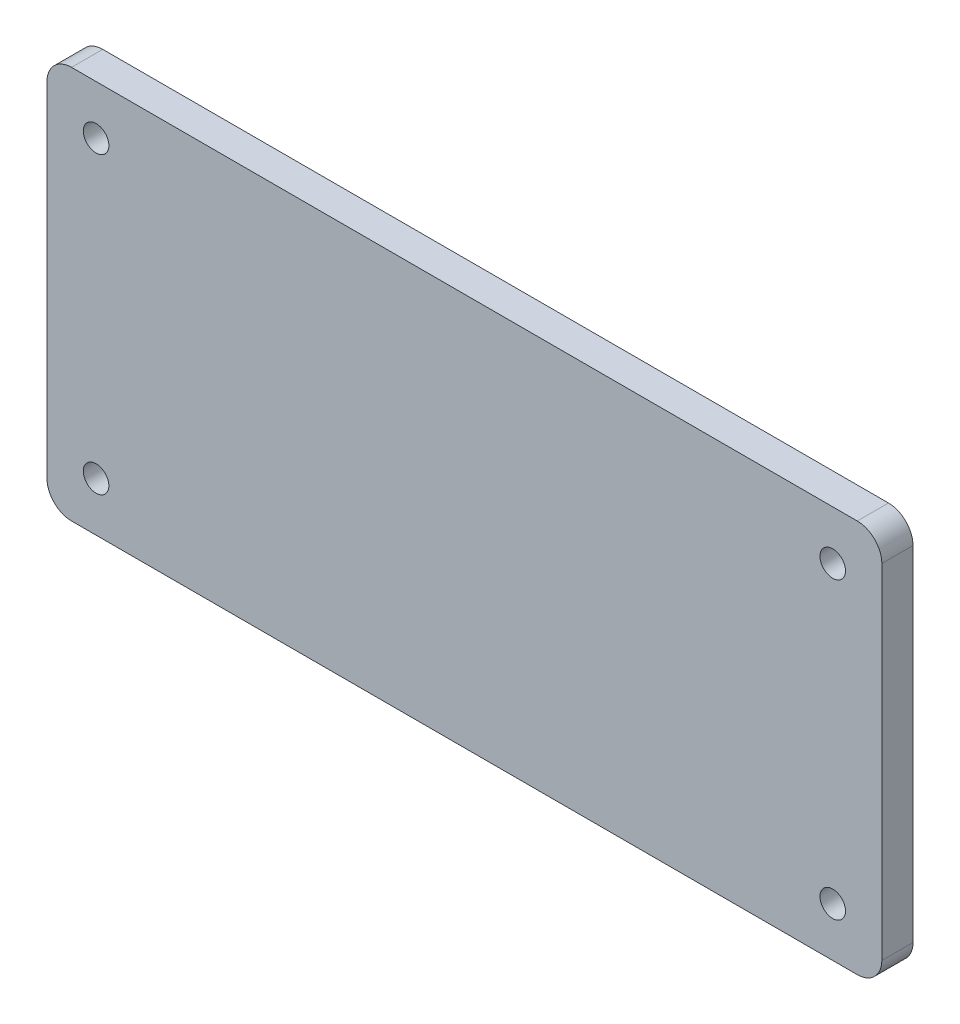
SolidWorks part; units mm, degrees
ref_plane "Front Plane" through (0, 0, 0) normal (0, 0, 1) x (1, 0, 0)
ref_plane "Top Plane" through (0, 0, 0) normal (0, 1, 0) x (1, 0, 0)
ref_plane "Right Plane" through (0, 0, 0) normal (1, 0, 0) x (0, 0, -1)
sketch "Sketch1" plane through (0, 0, 0) normal (0, 0, 1) x (1, 0, 0)
  line L0 (0, 124.4013) -> (0, -139.7481) construction
  line L1 (80, -40) -> (-80, -40)
  line L2 (85, -35) -> (85, 35)
  line L3 (80, 40) -> (-80, 40)
  line L4 (-85, -35) -> (-85, 35)
  line L5 (85, -40) -> (-85, 40) construction
  line L6 (85, 40) -> (-85, -40) construction
  line L7 (232.754, 0) -> (-222.1699, 0) construction
  circle A0 centre (-75, 30) radius 2.6
  circle A1 centre (75, 30) radius 2.6
  circle A2 centre (75, -30) radius 2.6
  circle A3 centre (-75, -30) radius 2.6
  arc A4 (80, 40) -> (85, 35) centre (80, 35) cw
  arc A5 (80, -40) -> (85, -35) centre (80, -35) ccw
  arc A6 (-80, -40) -> (-85, -35) centre (-80, -35) cw
  arc A7 (-85, 35) -> (-80, 40) centre (-80, 35) cw
  point P0 (0, 0)
  dimension "D5" = 5.2
  dimension "D6" = 5
  dimension "D1" = 80
  dimension "D2" = 170
  dimension "D3" = 10
  dimension "D4" = 10
extrude "Boss-Extrude1" add sketch "Sketch1" along normal blind 6.35
sketch "Sketch6" [suppressed] plane through (0, 0, 6.35) normal (0, 0, 1) x (1, 0, 0)
  line L0 (19, 0) -> (-19, 0) construction
  line B0 (-19, 14) -> (19, 14)
  line B1 (19, -14) -> (-19, -14)
  line B2 (19, 14) -> (19, -14)
  line B3 (-19, -14) -> (-19, 14)
  circle B4 centre (-14.5, -12.5) radius 1
  circle B5 centre (17.5, 12.5) radius 1
  line B6 (-19, 14) -> (-19, -14)
  circle B7 centre (-14.5, 12.5) radius 1
  circle B8 centre (17.5, -12.5) radius 1
sketch_block_instance "Block-Single_Motor_Driver_reference-1"
sketch_block "Block-Single_Motor_Driver_reference"
sketch_block_instance "Block-Single_Motor_Driver_reference-3"
sketch "Sketch7" [suppressed] plane through (0, 0, 6.35) normal (0, 0, 1) x (1, 0, 0)
  line B0 (10, 88.2866) -> (10, -79.1784) construction
  line B1 (-30.7948, 22.4079) -> (-30.7948, -19.5021)
  line B2 (-24.4448, -25.8521) -> (42.8652, -25.8521)
  circle B3 centre (-16.1898, 25.5829) radius 1.524
  arc B4 (-30.7948, -19.5021) -> (-24.4448, -25.8521) centre (-24.4448, -19.5021) ccw
  circle B5 centre (49.8502, 22.4079) radius 1.524
  circle B6 centre (49.8502, -19.5021) radius 1.524
  circle B7 centre (-16.1898, -22.6771) radius 1.524
  dimension "D1" = 10
sketch_block_instance "Block-BBB_reference-1"
sketch_block "Block-BBB_reference"
hole_wizard "BBB_mtg_holes" [suppressed] positions "Sketch3" profile "Sketch2" countersink size "M3" standard "ANSI Metric"
sketch "Sketch3" plane through (0, 0, 6.35) normal (0, 0, 1) x (1, 0, 0)
  point P0 (-16.1898, 25.5829)
  point P2 (-16.1898, -22.6771)
  point P4 (49.8502, -19.5021)
  point P6 (49.8502, 22.4079)
sketch "Sketch2" plane through (-16.1898, 25.5829, 6.35) normal (1, 0, 0) x (0, -1, 0)
  line L0 (0, 0) -> (0, 6.35)
  line L1 (0, 6.35) -> (1.7, 6.35)
  line L2 (1.7, 6.35) -> (1.7, 1.45)
  line L3 (1.7, 1.45) -> (3.15, 0)
  line L5 (3.15, 0) -> (0, 0)
  line L6 (-1.7, 1.45) -> (-3.15, 0) construction
  line L11 (0, -6.35) -> (0, 107.95) construction
  dimension "Thru Hole Dia." = 3.4
  dimension "Thru Hole Depth" = 6.35
  dimension "Near C'Sink Dia." = 6.3
  dimension "Near C'Sink Angle" = 90
hole_wizard "Motor_Driver_mtg_holes" [suppressed] positions "Sketch5" profile "Sketch4" countersink size "#0" standard "ANSI Inch"
sketch "Sketch5" plane through (0, 0, 6.35) normal (0, 0, 1) x (1, 0, 0)
  point P0 (17.5, 12.5)
  point P2 (-14.5, -12.5)
  point P7 (-14.5, 12.5)
  point P10 (17.5, -12.5)
sketch "Sketch4" plane through (17.5, 12.5, 6.35) normal (1, 0, 0) x (0, -1, 0)
  line L0 (0, 0) -> (0, 6.35)
  line L1 (0, 6.35) -> (0.889, 6.35)
  line L2 (0.889, 6.35) -> (0.889, 0.5222)
  line L3 (0.889, 0.5222) -> (1.5113, 0)
  line L5 (1.5113, 0) -> (0, 0)
  line L6 (-0.889, 0.5222) -> (-1.5113, 0) construction
  line L11 (0, -6.35) -> (0, 107.95) construction
  dimension "Thru Hole Dia." = 1.778
  dimension "Thru Hole Depth" = 6.35
  dimension "Near C'Sink Dia." = 3.0226
  dimension "Near C'Sink Angle" = 100
hole_wizard "Voltage_Converter_mtg_holes" [suppressed] positions "Sketch9" profile "Sketch8" countersink size "M3" standard "ANSI Metric"
sketch "Sketch9" plane through (0, 0, 6.35) normal (0, 0, 1) x (1, 0, 0)
  line L0 (0, 47.6195) -> (0, -55.3004) construction
  line L2 (-92.1724, 0) -> (102.7945, 0) construction
  point P0 (-20, 0)
  point P2 (20, 0)
  dimension "D1" = 46
  dimension "D2" = 30
sketch "Sketch8" plane through (-20, 0, 6.35) normal (1, 0, 0) x (0, -1, 0)
  line L0 (0, 0) -> (0, 6.35)
  line L1 (0, 6.35) -> (1.7, 6.35)
  line L2 (1.7, 6.35) -> (1.7, 1.45)
  line L3 (1.7, 1.45) -> (3.15, 0)
  line L5 (3.15, 0) -> (0, 0)
  line L6 (-1.7, 1.45) -> (-3.15, 0) construction
  line L11 (0, -6.35) -> (0, 107.95) construction
  dimension "Thru Hole Dia." = 3.4
  dimension "Thru Hole Depth" = 6.35
  dimension "Near C'Sink Dia." = 6.3
  dimension "Near C'Sink Angle" = 90
chamfer "Chamfer1" [suppressed] distance 3 angle 45
equation "\"motor_module_height\"= 80"
equation "\"motor_module_width\"= 80"
equation "\"motor_module_length\"= 170"
equation "\"D1@Sketch1\"=\"motor_module_height\""
equation "\"D2@Sketch1\"=\"motor_module_length\""
equation "\"D4@Sketch1\"=\"D3@Sketch1\""
